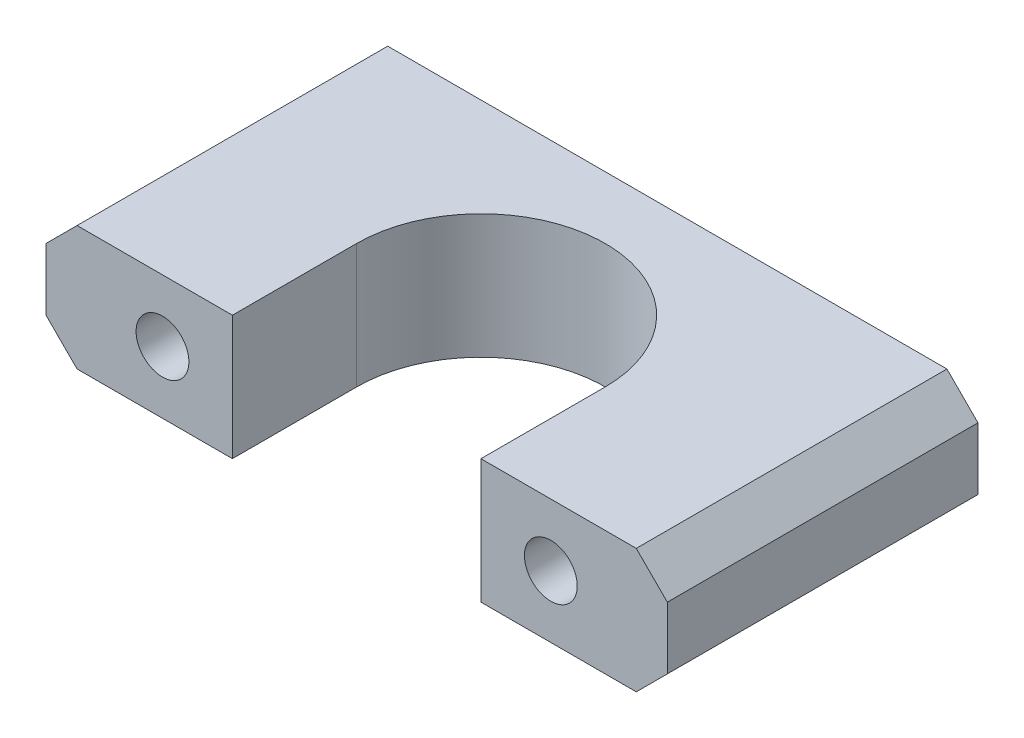
SolidWorks part; units mm, degrees
ref_plane "Front Plane" through (0, 0, 0) normal (0, 0, 1) x (1, 0, 0)
ref_plane "Top Plane" through (0, 0, 0) normal (0, 1, 0) x (1, 0, 0)
ref_plane "Right Plane" through (0, 0, 0) normal (1, 0, 0) x (0, 0, -1)
sketch "Sketch2" plane through (0, 0, 0) normal (0, 1, 0) x (1, 0, 0)
  line L1 (0, 0) -> (40, 0)
  line L2 (0, 0) -> (0, 20)
  line L3 (0, 20) -> (40, 20)
  line L4 (40, 0) -> (40, 20)
  dimension "D1" = 20
  dimension "D2" = 40
extrude "Boss-Extrude1" add sketch "Sketch2" along normal blind 8
sketch "Sketch3" plane through (0, 0, 0) normal (0, -1, 0) x (1, 0, 0)
  line L0 (20, 0) -> (20, -13.6187) construction
  line L1 (0, 0) -> (40, 0) construction
  line L2 (12, -8) -> (12, 0)
  line L3 (12, 0) -> (28, 0)
  line L4 (28, 0) -> (28, -8)
  arc A0 (12, -8) -> (28, -8) centre (20, -8) ccw
  dimension "D1" = 8
  dimension "D2" = 8
extrude "Cut-Extrude1" cut sketch "Sketch3" against normal through all
sketch "Sketch4" plane through (0, 0, 0) normal (0, 0, 1) x (1, 0, 0)
  line L0 (0, 4) -> (40, 4) construction
  line L1 (0, 8) -> (0, 0) construction
  line L2 (40, 8) -> (40, 0) construction
  line L3 (20, 0) -> (20, 8) construction
  line L4 (12, 0) -> (28, 0) construction
  line L5 (28, 8) -> (12, 8) construction
  circle A0 centre (7.5, 4) radius 1.7
  circle A1 centre (32.5, 4) radius 1.7
  dimension "D1" = 3.4
  dimension "D2" = 12.5
extrude "Cut-Extrude2" cut sketch "Sketch4" against normal through all
chamfer "Chamfer1" distance 2 angle 45 4 edges at (40, 8, -10) (40, 0, -10) (0, 8, -10) (0, 0, -10)
